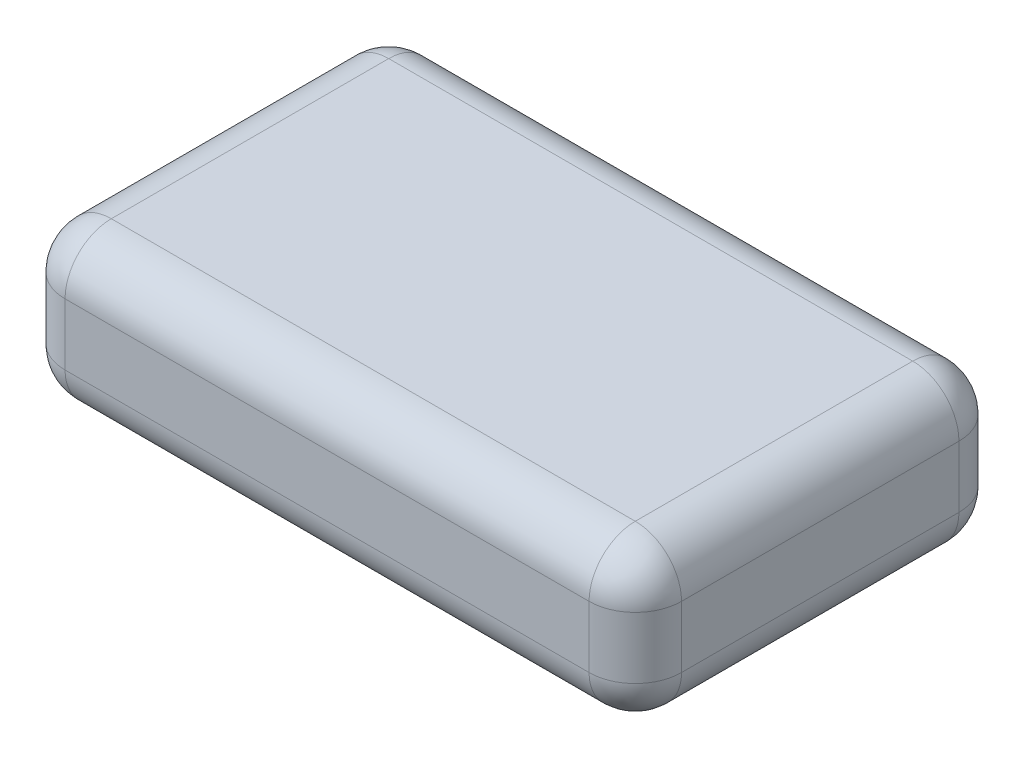
SolidWorks part; units mm, degrees
ref_plane "Front Plane" through (0, 0, 0) normal (0, 0, 1) x (1, 0, 0)
ref_plane "Top Plane" through (0, 0, 0) normal (0, 1, 0) x (1, 0, 0)
ref_plane "Right Plane" through (0, 0, 0) normal (1, 0, 0) x (0, 0, -1)
sketch "Sketch1" plane through (0, 0, 0) normal (0, 1, 0) x (1, 0, 0)
  line L1 (-127, -76.2) -> (127, -76.2)
  line L2 (-127, -76.2) -> (-127, 76.2)
  line L3 (-127, 76.2) -> (127, 76.2)
  line L4 (127, -76.2) -> (127, 76.2)
  line L5 (-127, -76.2) -> (127, 76.2) construction
  line L6 (-127, 76.2) -> (127, -76.2) construction
  point P0 (0, 0)
  dimension "D1" = 254
  dimension "D2" = 152.4
extrude "Boss-Extrude1" add sketch "Sketch1" along normal blind 63.5
fillet "Fillet1" radius 19.05 12 edges at (0, 63.5, -76.2) (0, 0, -76.2) (0, 63.5, 76.2) (0, 0, 76.2) (127, 31.75, 76.2) (127, 63.5, 0) (127, 31.75, -76.2) (127, 0, 0) (-127, 31.75, -76.2) (-127, 63.5, 0) (-127, 31.75, 76.2) (-127, 0, 0)
